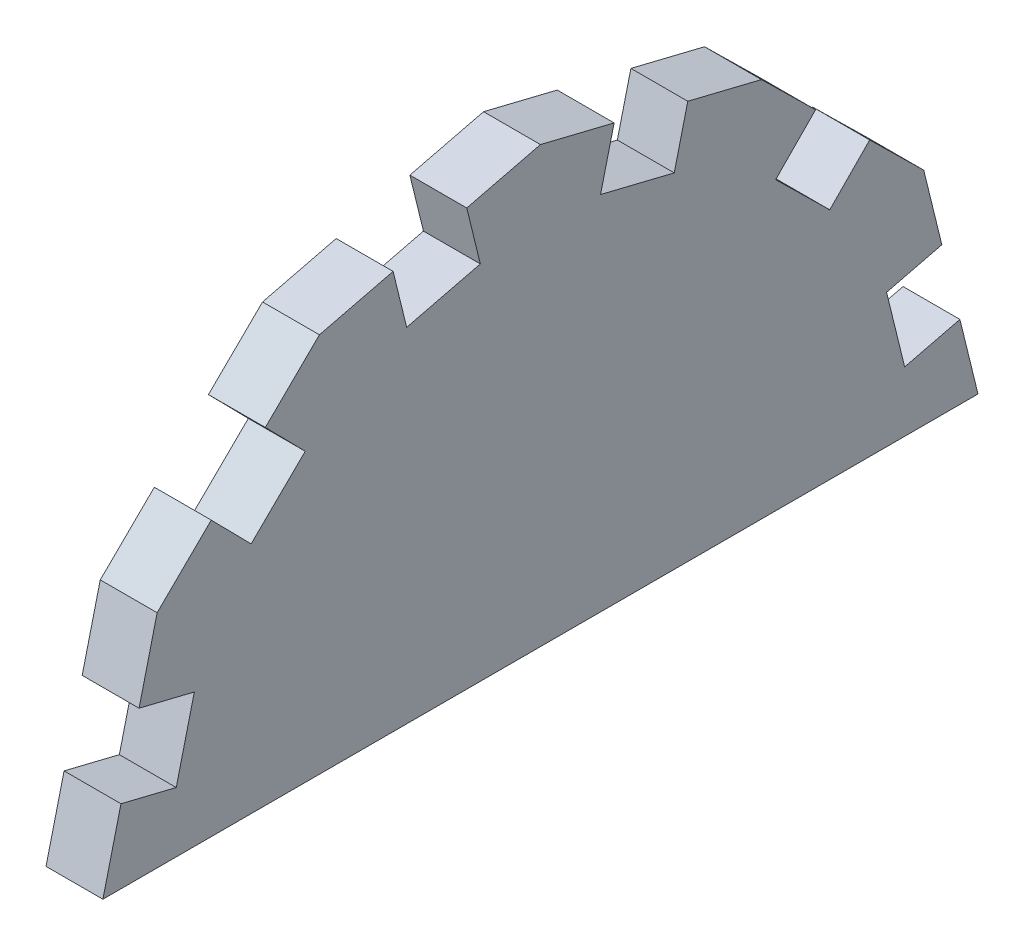
SolidWorks part; units mm, degrees
ref_plane "Front Plane" through (0, 0, 0) normal (0, 0, 1) x (1, 0, 0)
ref_plane "Top Plane" through (0, 0, 0) normal (0, 1, 0) x (1, 0, 0)
ref_plane "Right Plane" through (0, 0, 0) normal (1, 0, 0) x (0, 0, -1)
sketch "Sketch2" plane through (0, 0, 0) normal (1, 0, 0) x (0, 0, -1)
  line L0 (80.5781, 0) -> (-80.5781, 0) construction
  line L5 (0, 40.0374) -> (0, -40.0374) construction
  line L6 (-73.2528, 0) -> (73.2528, 0) construction
  line L7 (-64.1702, 37.0016) -> (-37.0016, 63.7125) construction
  line L8 (-37.0016, 63.7125) -> (0, 72.7952) construction
  line L9 (-73.2528, 0) -> (-64.1702, 37.0016) construction
  line L10 (-64.1702, 37.0016) -> (-73.2528, 0) construction
  line L11 (-37.0016, 63.7125) -> (0, 72.7952) construction
  line L12 (37.0016, 63.7125) -> (0, 72.7952) construction
  line L13 (64.1702, 37.0016) -> (37.0016, 63.7125) construction
  line L14 (64.1702, 37.0016) -> (73.2528, 0) construction
  line L15 (37.0016, 63.7125) -> (64.1702, 37.0016) construction
  line L16 (73.2528, 0) -> (-73.2528, 0) construction
  line L17 (-73.2528, 0) -> (-64.1702, 37.0016)
  line L18 (-64.1702, 37.0016) -> (-37.0016, 63.7125)
  line L19 (-37.0016, 63.7125) -> (0, 72.7952)
  line L20 (0, 72.7952) -> (37.0016, 63.7125)
  line L21 (37.0016, 63.7125) -> (64.1702, 37.0016)
  line L22 (64.1702, 37.0016) -> (73.2528, 0)
  line L23 (73.2528, 0) -> (-73.2528, 0)
  dimension "D1" = 76.208
  dimension "D2" = 148.305
  dimension "D3" = 38.1
  dimension "D4" = 38.1
  dimension "D5" = 38.1
extrude "Boss-Extrude1" add sketch "Sketch2" along normal blind 9.525
sketch "Sketch3" plane through (0, 16.9593, 69.0899) normal (0, 0.2384, 0.9712) x (1, 0, 0)
  line L0 (0, 20.6372) -> (0, -17.4628) construction
  line L1 (0, -4.7628) -> (9.525, -4.7628)
  line L2 (0, -4.7628) -> (0, 7.9372)
  line L3 (0, 7.9372) -> (9.525, 7.9372)
  line L4 (9.525, -4.7628) -> (9.525, 7.9372)
  line L5 (9.525, 20.6372) -> (9.525, -17.4628) construction
  line L6 (9.525, -17.4628) -> (0, -17.4628) construction
  dimension "D1" = 12.7
  dimension "D2" = 12.7
extrude "Cut-Extrude1" cut sketch "Sketch3" against normal blind 9.525
sketch "Sketch4" plane through (0, 50.8955, 50.0382) normal (0, 0.7131, 0.7011) x (1, 0, 0)
  line L0 (0, 18.282) -> (0, -19.818) construction
  line L1 (0, -7.118) -> (9.525, -7.118)
  line L2 (0, -7.118) -> (0, 5.582)
  line L3 (0, 5.582) -> (9.525, 5.582)
  line L4 (9.525, -7.118) -> (9.525, 5.582)
  line L5 (9.525, 18.282) -> (9.525, -19.818) construction
  line L6 (9.525, -19.818) -> (0, -19.818) construction
  dimension "D1" = 12.7
  dimension "D2" = 12.7
extrude "Cut-Extrude2" cut sketch "Sketch4" against normal blind 9.525
sketch "Sketch5" plane through (0, 68.6583, 16.8534) normal (0, 0.9712, 0.2384) x (1, 0, 0)
  line L0 (0, 17.3537) -> (0, -20.7463) construction
  line L1 (0, -8.0463) -> (9.525, -8.0463)
  line L2 (0, -8.0463) -> (0, 4.6537)
  line L3 (0, 4.6537) -> (9.525, 4.6537)
  line L4 (9.525, -8.0463) -> (9.525, 4.6537)
  line L5 (9.525, 17.3537) -> (9.525, -20.7463) construction
  line L6 (9.525, -20.7463) -> (0, -20.7463) construction
  dimension "D1" = 12.7
  dimension "D2" = 12.7
extrude "Cut-Extrude3" cut sketch "Sketch5" against normal blind 9.525
mirror "Mirror1" about plane through (0, 0, 0) normal (0, 0, 1) of "Cut-Extrude1", "Cut-Extrude2", "Cut-Extrude3"
